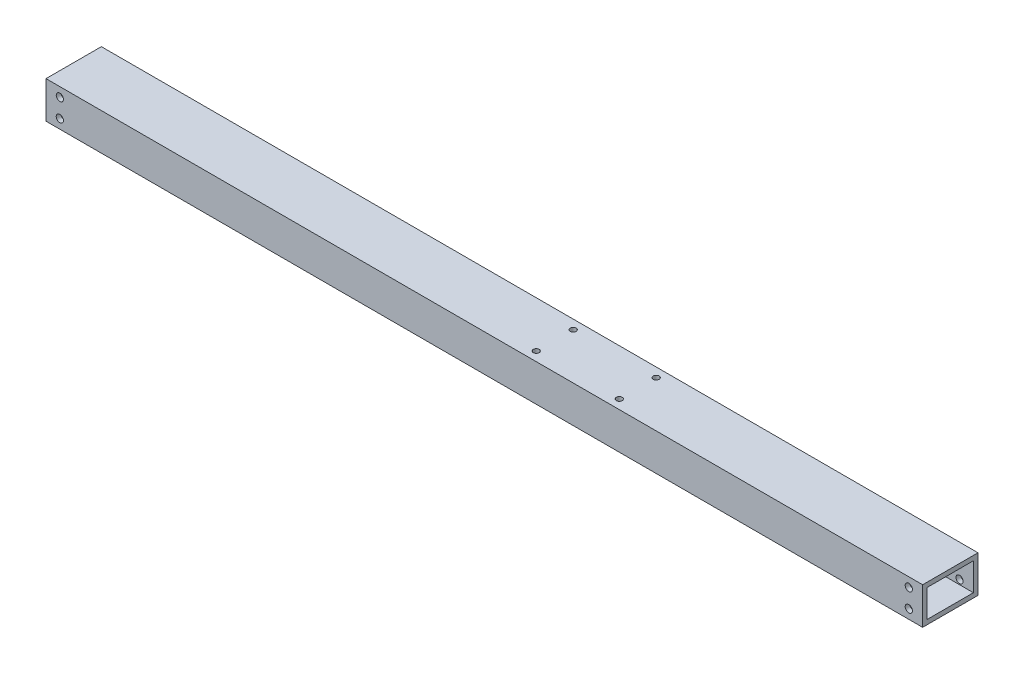
SolidWorks part; units mm, degrees
material "6061-T6 (SS)"
ref_plane "Front Plane" through (0, 0, 0) normal (0, 0, 1) x (1, 0, 0)
ref_plane "Top Plane" through (0, 0, 0) normal (0, 1, 0) x (1, 0, 0)
ref_plane "Right Plane" through (0, 0, 0) normal (1, 0, 0) x (0, 0, -1)
sketch "Sketch1" plane through (0, 0, 0) normal (1, 0, 0) x (0, 0, -1)
  line L0 (-15.875, 9.525) -> (-15.875, -9.525)
  line L1 (-19.05, 12.7) -> (19.05, 12.7)
  line L2 (-19.05, 12.7) -> (-19.05, -12.7)
  line L3 (-19.05, -12.7) -> (19.05, -12.7)
  line L4 (19.05, 12.7) -> (19.05, -12.7)
  line L5 (-19.05, 12.7) -> (19.05, -12.7) construction
  line L6 (-19.05, -12.7) -> (19.05, 12.7) construction
  line L7 (-15.875, -9.525) -> (15.875, -9.525)
  line L8 (15.875, 9.525) -> (15.875, -9.525)
  line L9 (-15.875, 9.525) -> (15.875, 9.525)
  point P0 (0, 0)
  dimension "D1" = 38.1
  dimension "D2" = 25.4
  dimension "D3" = 3.175
extrude "Boss-Extrude1" add sketch "Sketch1" along normal mid plane 603.25
sketch "Sketch2" plane through (0, 0, 19.05) normal (0, 0, 1) x (1, 0, 0)
  line L0 (-292.1, 12.7) -> (-292.1, -12.7) construction
  line L1 (301.625, 12.7) -> (-301.625, 12.7) construction
  line L2 (301.625, -12.7) -> (-301.625, -12.7) construction
  line L3 (-301.625, 12.7) -> (-301.625, -12.7) construction
  line L5 (-14.2875, 12.7) -> (14.2875, 12.7) construction
  line L6 (-14.2875, 12.7) -> (-14.2875, 9.525) construction
  line L7 (-14.2875, 9.525) -> (14.2875, 9.525) construction
  line L8 (14.2875, 12.7) -> (14.2875, 9.525) construction
  circle A0 centre (-292.1, 6.35) radius 2.4892
  circle A1 centre (-292.1, -6.35) radius 2.4892
  point P17 (0, 12.7)
  point P18 (0, 12.7)
  dimension "D2" = 12.7
  dimension "D3" = 6.35
  dimension "D4" = 4.9784
  dimension "D1" = 9.525
  dimension "D5" = 28.575
  dimension "D6" = 3.175
extrude "Cut-Extrude1" cut sketch "Sketch2" against normal through all
mirror "Mirror1" about plane through (0, 0, 0) normal (1, 0, 0) of "Cut-Extrude1"
sketch "Sketch4" plane through (0, -12.7, 0) normal (0, -1, 0) x (1, 0, 0)
  circle A0 centre (86.5502, -12.7) radius 2.0193 construction
  circle A1 centre (86.5502, 12.7) radius 2.0193 construction
  circle A2 centre (29.4002, 12.7) radius 2.0193 construction
  circle A3 centre (29.4002, -12.7) radius 2.0193 construction
  circle A4 centre (86.5502, -12.7) radius 2.0193
  circle A5 centre (86.5502, 12.7) radius 2.0193
  circle A6 centre (29.4002, 12.7) radius 2.0193
  circle A7 centre (29.4002, -12.7) radius 2.0193
extrude "Cut-Extrude2" cut sketch "Sketch4" against normal through all
equation "\"Thick\"= \"in\""
